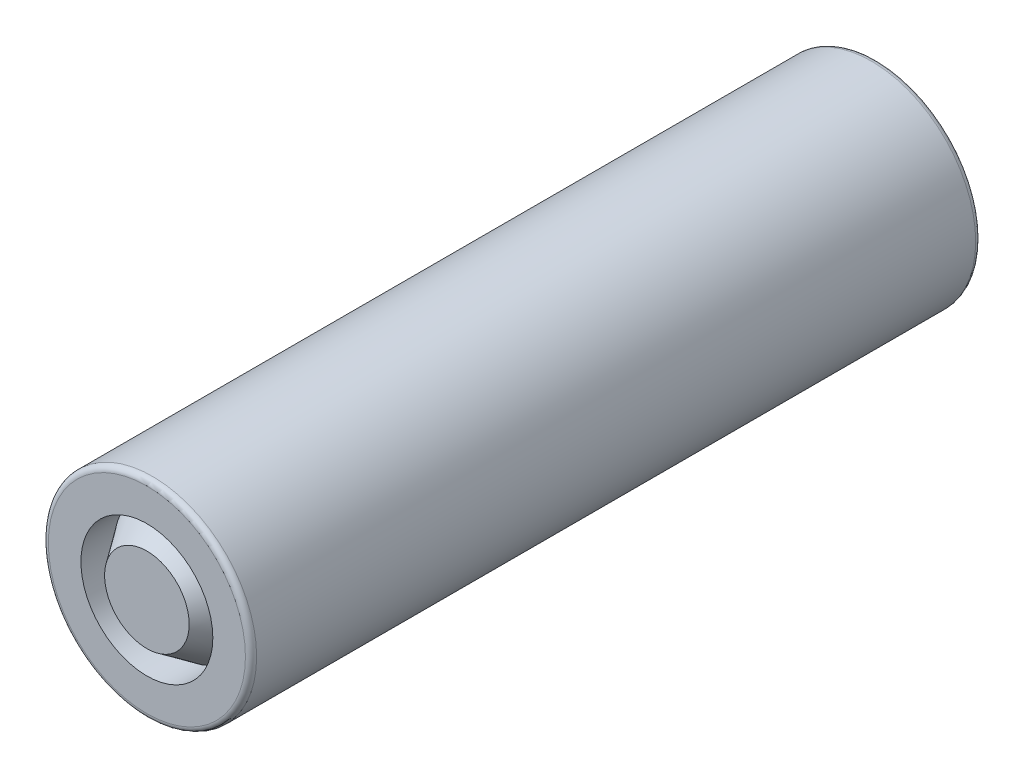
SolidWorks part; units mm, degrees
material "6061-T6 (SS)"
ref_plane "Front Plane" through (0, 0, 0) normal (0, 0, 1) x (1, 0, 0)
ref_plane "Top Plane" through (0, 0, 0) normal (0, 1, 0) x (1, 0, 0)
ref_plane "Right Plane" through (0, 0, 0) normal (1, 0, 0) x (0, 0, -1)
ref_axis "Axis1" through (0, 0, 55) along (0, 0, -1)
sketch "Sketch1" plane through (0, 0, 0) normal (0, 0, 1) x (1, 0, 0)
  circle A0 centre (0, 0) radius 9.3
  dimension "D1" = 18.6
extrude "Boss-Extrude1" add sketch "Sketch1" against normal blind 65.2 contours A0
sketch "Sketch3" plane through (0, 0, 0) normal (1, 0, 0) x (0, 0, -1)
  line L0 (0, 5.89) -> (0, 3.775)
  line L1 (0, 9.3) -> (0, -9.3) construction
  line L2 (0, 3.775) -> (3, 5.89)
  line L3 (3, 5.89) -> (0, 5.89)
  line L4 (65.2, 9.3) -> (0, 9.3) construction
  dimension "D1" = 3.775
  dimension "D2" = 3
  dimension "D3" = 3.41
revolve "Cut-Revolve1" cut sketch "Sketch3" angle 360 about axis through (0, 0, 55) along (0, 0, -1)
fillet "Fillet1" radius 0.5 2 edges at (9.3, 0, -65.2) (9.3, 0, 0)
